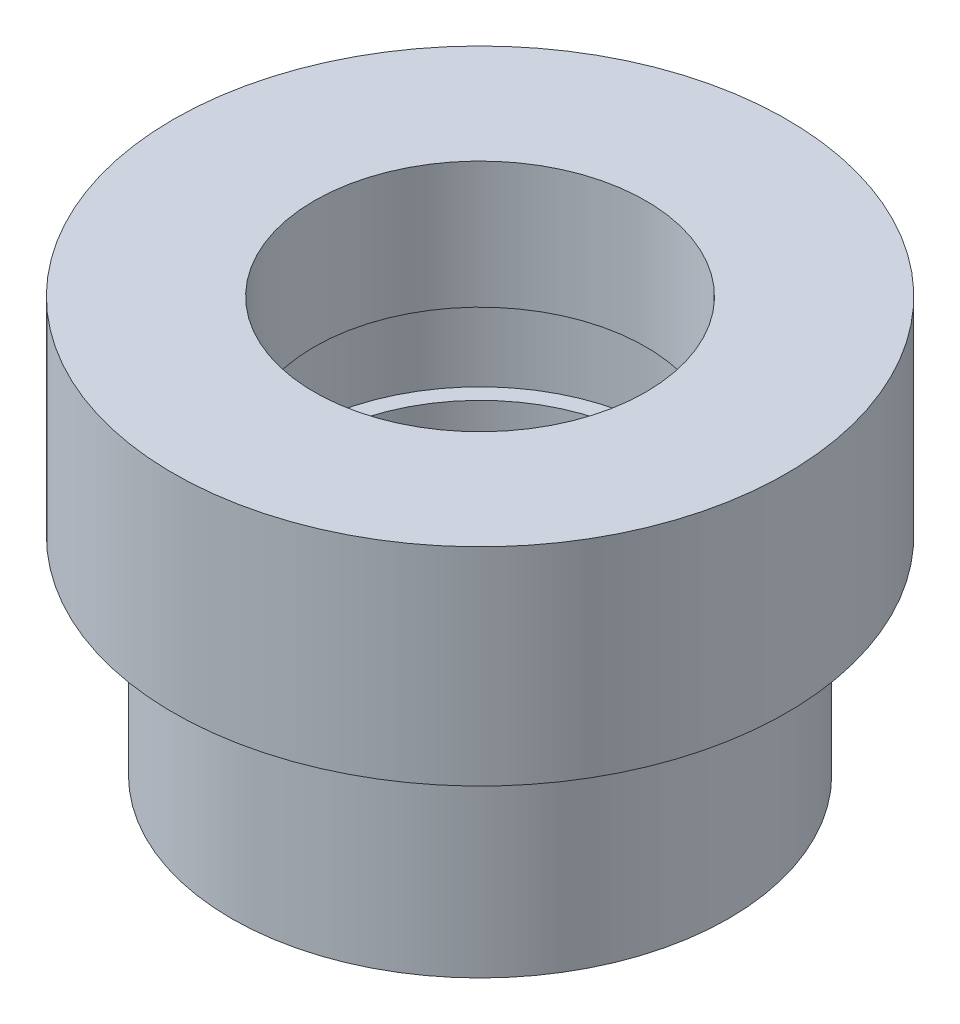
SolidWorks part; units mm, degrees
ref_plane "Front Plane" through (0, 0, 0) normal (0, 0, 1) x (1, 0, 0)
ref_plane "Top Plane" through (0, 0, 0) normal (0, 1, 0) x (1, 0, 0)
ref_plane "Right Plane" through (0, 0, 0) normal (1, 0, 0) x (0, 0, -1)
sketch "Sketch6" plane through (0, 0, 0) normal (0, 0, 1) x (1, 0, 0)
  line L0 (-84.3175, 64.6709) -> (-84.3175, 39.6709)
  line L1 (-84.3175, 39.6709) -> (-77.3175, 39.6709)
  line L2 (-77.3175, 39.6709) -> (-77.3175, 14.6709)
  line L3 (-77.3175, 14.6709) -> (-67.3175, 14.6709)
  line L4 (-67.3175, 14.6709) -> (-67.3175, 39.6709)
  line L5 (-67.3175, 39.6709) -> (-69.3175, 39.6709)
  line L6 (-69.3175, 39.6709) -> (-69.3175, 49.4048)
  line L7 (-69.3175, 49.4048) -> (-67.3175, 49.4048)
  line L8 (-67.3175, 49.4048) -> (-67.3175, 64.6709)
  line L9 (-67.3175, 64.6709) -> (-84.3175, 64.6709)
  line L10 (-47.3175, 64.6709) -> (-47.3175, -3.3487) construction
  dimension "D1" = 25
  dimension "D2" = 25
  dimension "D3" = 10
  dimension "D4" = 25
  dimension "D5" = 15
  dimension "D6" = 7
  dimension "D7" = 2
  dimension "D8" = 20
revolve "Revolve2" add sketch "Sketch6" angle 360 about L10
